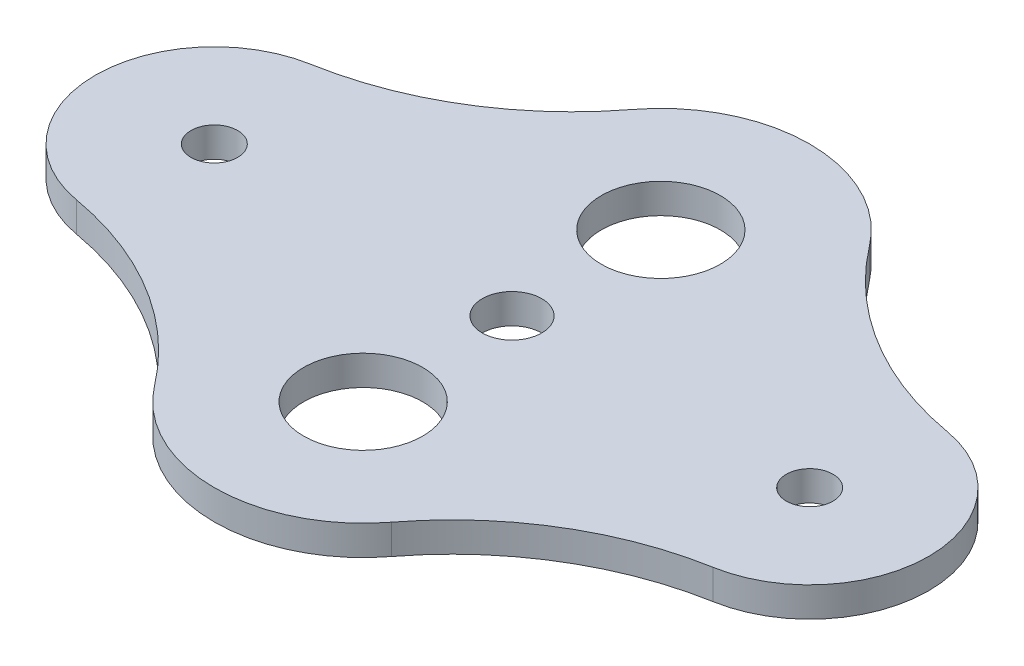
SolidWorks part; units mm, degrees
ref_plane "Front Plane" through (0, 0, 0) normal (0, 0, 1) x (1, 0, 0)
ref_plane "Top Plane" through (0, 0, 0) normal (0, 1, 0) x (1, 0, 0)
ref_plane "Right Plane" through (0, 0, 0) normal (1, 0, 0) x (0, 0, -1)
sketch "Sketch1" plane through (0, 0, 0) normal (0, 1, 0) x (1, 0, 0)
  arc A3 (12.6274, 25.496) -> (-12.6274, 25.496) centre (0, 15.875) ccw
  arc A4 (-12.6274, -25.496) -> (12.6274, -25.496) centre (0, -15.875) ccw
  arc A5 (-33.9534, 12.5074) -> (-33.9534, -12.5074) centre (-31.75, 0) ccw
  arc A6 (33.9534, -12.5074) -> (33.9534, 12.5074) centre (31.75, 0) ccw
  arc A7 (-12.6274, 25.496) -> (-33.9534, 12.5074) centre (-39.9027, 46.2774) cw
  arc A8 (-33.9534, -12.5074) -> (-12.6274, -25.496) centre (-39.9027, -46.2774) cw
  arc A9 (12.6274, 25.496) -> (33.9534, 12.5074) centre (39.9027, 46.2774) ccw
  arc A10 (12.6274, -25.496) -> (33.9534, -12.5074) centre (39.9027, -46.2774) cw
  dimension "D1" = 31.75
  dimension "D2" = 63.5
  dimension "D3" = 25.4
  dimension "D4" = 31.75
  dimension "D5" = 34.29
extrude "Boss-Extrude1" add sketch "Sketch1" along normal blind 3.175
hole_wizard "1/4 (0.25) Diameter Hole1" positions "Sketch3" profile "Sketch4" hole size "1/4" standard "ANSI Inch" end condition through all
sketch "Sketch3" plane through (0, 3.175, 0) normal (0, 1, 0) x (1, 0, 0)
  point P0 (0, 0)
sketch "Sketch4" plane through (0, 3.175, 0) normal (1, 0, 0) x (0, 0, 1)
  line L0 (0, 0) -> (0, 3.175)
  line L1 (0, 3.175) -> (3.175, 3.175)
  line L2 (3.175, 3.175) -> (3.175, 0)
  line L5 (3.175, 0) -> (0, 0)
  line L11 (0, -6.35) -> (0, 107.95) construction
  dimension "Thru Hole Dia." = 6.35
  dimension "Thru Hole Depth" = 3.175
sketch "Sketch5" plane through (0, 3.175, 0) normal (0, 1, 0) x (1, 0, 0)
  circle A0 centre (0, 15.875) radius 6.35
  circle A1 centre (0, -15.875) radius 6.35
  arc A2 (12.6274, 25.496) -> (-12.6274, 25.496) centre (0, 15.875) ccw construction
  arc A3 (-12.6274, -25.496) -> (12.6274, -25.496) centre (0, -15.875) ccw construction
  dimension "D1" = 12.7
extrude "Cut-Extrude1" cut sketch "Sketch5" against normal through all
sketch "Sketch6" plane through (0, 3.175, 0) normal (0, 1, 0) x (1, 0, 0)
  circle A0 centre (-31.75, 0) radius 2.4892
  circle A1 centre (31.75, 0) radius 2.4892
  arc A4 (-33.9534, 12.5074) -> (-33.9534, -12.5074) centre (-31.75, 0) ccw construction
  arc A5 (33.9534, -12.5074) -> (33.9534, 12.5074) centre (31.75, 0) ccw construction
  point P4 (0, 0)
  point P6 (0, 0)
  dimension "D1" = 4.9784
extrude "Cut-Extrude2" cut sketch "Sketch6" against normal through all
